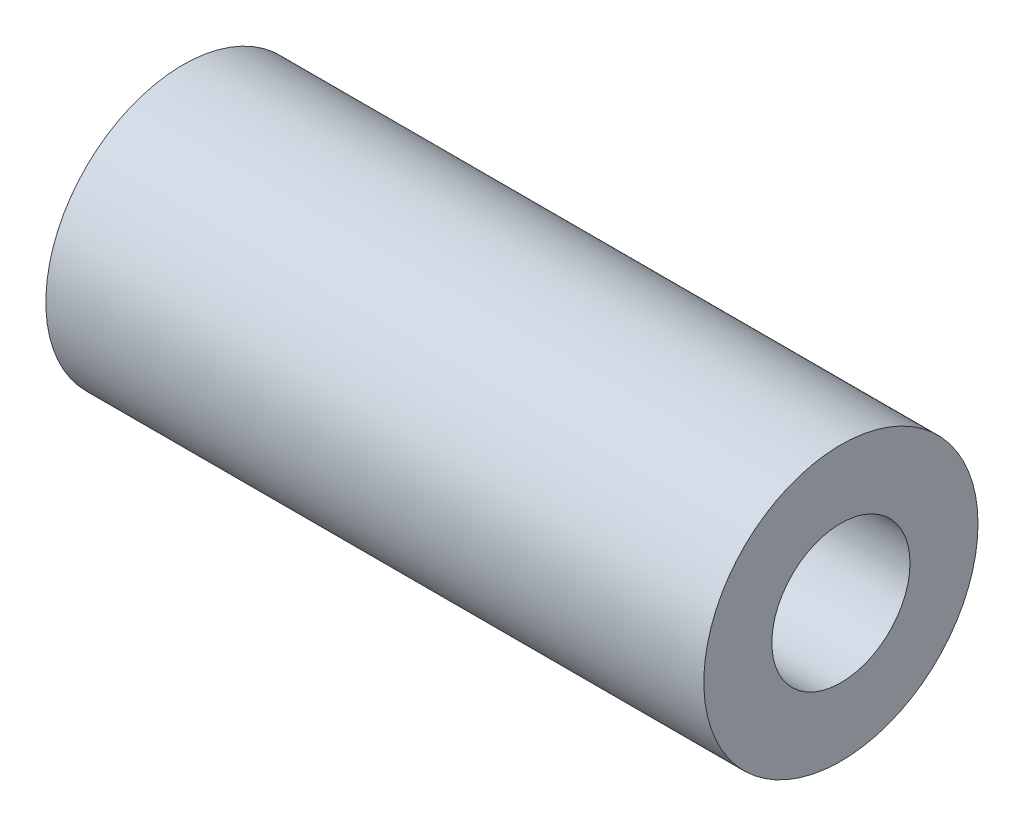
SolidWorks part; units mm, degrees
material "Nylon 101"
ref_plane "Front Plane" through (0, 0, 0) normal (0, 0, 1) x (1, 0, 0)
ref_plane "Top Plane" through (0, 0, 0) normal (0, 1, 0) x (1, 0, 0)
ref_plane "Right Plane" through (0, 0, 0) normal (1, 0, 0) x (0, 0, -1)
sketch "Sketch1" plane through (0, 0, 0) normal (1, 0, 0) x (0, 0, -1)
  circle A0 centre (0, 0) radius 3.2004
  circle A1 centre (0, 0) radius 6.35
  dimension "D1" = 12.7
  dimension "D2" = 6.4008
extrude "Boss-Extrude1" add sketch "Sketch1" along normal blind 30.48
